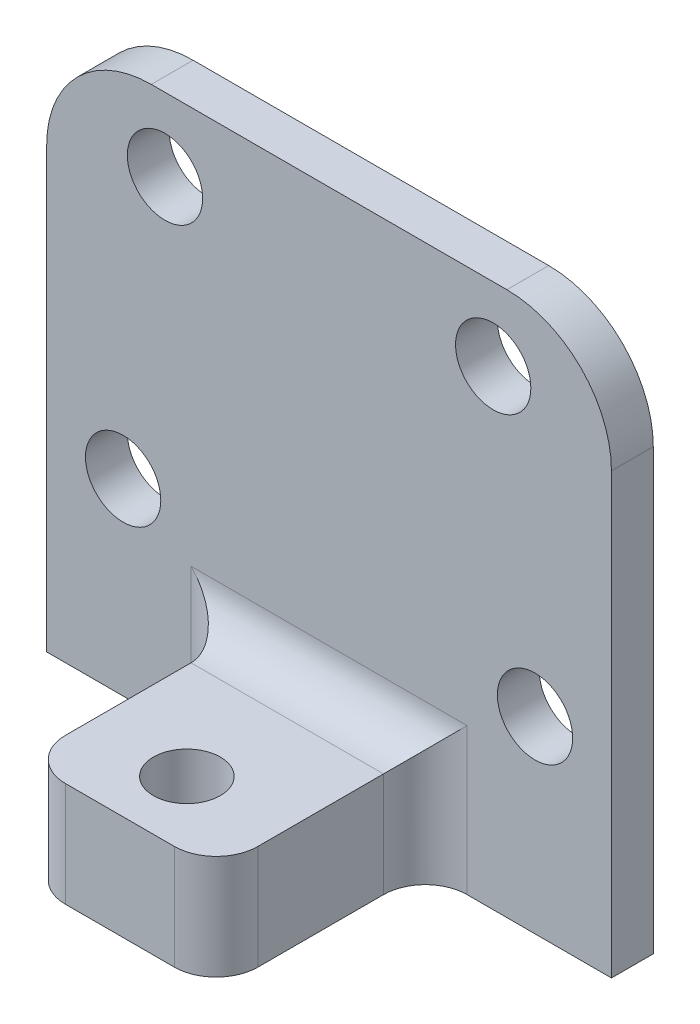
SolidWorks part; units mm, degrees
ref_plane "Front" through (0, 0, 0) normal (0, 0, 1) x (1, 0, 0)
ref_plane "Top" through (0, 0, 0) normal (0, 1, 0) x (1, 0, 0)
ref_plane "Right" through (0, 0, 0) normal (1, 0, 0) x (0, 0, -1)
sketch "Sketch1" plane through (0, 0, 0) normal (0, 0, 1) x (1, 0, 0)
  line L0 (13.5, 21) -> (13.5, 0) construction
  line L1 (-13.5, 26) -> (13.5, 26)
  line L2 (-13.5, 26) -> (-13.5, 0)
  line L3 (-13.5, 0) -> (13.5, 0)
  line L4 (13.5, 26) -> (13.5, 0)
  line L5 (-8.5, 26) -> (8.5, 26) construction
extrude "Boss-Extrude1" add sketch "Sketch1" along normal blind 2
sketch "Sketch2" plane through (0, 0, 2) normal (0, 0, 1) x (1, 0, 0)
  line L0 (13.5, 0) -> (13.5, 26) construction
  line L1 (-13.5, 0) -> (13.5, 0)
  line L2 (-13.5, 0) -> (-13.5, 5)
  line L3 (-13.5, 5) -> (13.5, 5)
  line L4 (13.5, 0) -> (13.5, 5)
  dimension "D1" = 5
extrude "Boss-Extrude2" add sketch "Sketch2" along normal blind 10
sketch "Sketch3" plane through (0, 0, 0) normal (0, -1, 0) x (1, 0, 0)
  circle A0 centre (0, 8.8) radius 1.6 construction
  circle A1 centre (0, 8.8) radius 1.6
extrude "Cut-Extrude1" cut sketch "Sketch3" against normal up to next
sketch "Sketch4" plane through (0, 5, 0) normal (0, 1, 0) x (1, 0, 0)
  line L0 (13.5, -2) -> (-13.5, -2) construction
  line L1 (13.5, -12) -> (4.6, -12)
  line L2 (13.5, -12) -> (13.5, -2)
  line L3 (13.5, -2) -> (4.6, -2)
  line L4 (4.6, -12) -> (4.6, -2)
  line L5 (1.6, -12) -> (1.6, -2) construction
  line L6 (13.5, -12) -> (-13.5, -12) construction
  line L7 (13.5, -2) -> (-13.5, -2) construction
  circle A0 centre (0, -8.8) radius 1.6 construction
  dimension "D1" = 3
extrude "Cut-Extrude2" cut sketch "Sketch4" against normal up to next (5 mm away)
mirror "Mirror1" about plane through (0, 0, 0) normal (1, 0, 0) of "Cut-Extrude2"
sketch "Sketch5" plane through (0, 0, 0) normal (0, 0, -1) x (-1, 0, 0)
  circle A0 centre (-7.8459, 22.5) radius 1.8 construction
  circle A1 centre (7.8459, 22.5) radius 1.8 construction
  circle A2 centre (-9.8466, 9) radius 1.8 construction
  circle A3 centre (9.8466, 9) radius 1.8 construction
  circle A4 centre (-7.8459, 22.5) radius 1.8
  circle A5 centre (7.8459, 22.5) radius 1.8
  circle A6 centre (-9.8466, 9) radius 1.8
  circle A7 centre (9.8466, 9) radius 1.8
extrude "Cut-Extrude3" cut sketch "Sketch5" against normal up to next
fillet "Fillet1" radius 5 2 edges at (-13.5, 26, 1) (13.5, 26, 1)
fillet "Fillet2" radius 2 3 edges at (-4.6, 2.5, 2) (4.6, 2.5, 2)
fillet "Fillet3" radius 2 2 edges at (-4.6, 2.5, 12) (4.6, 2.5, 12)
